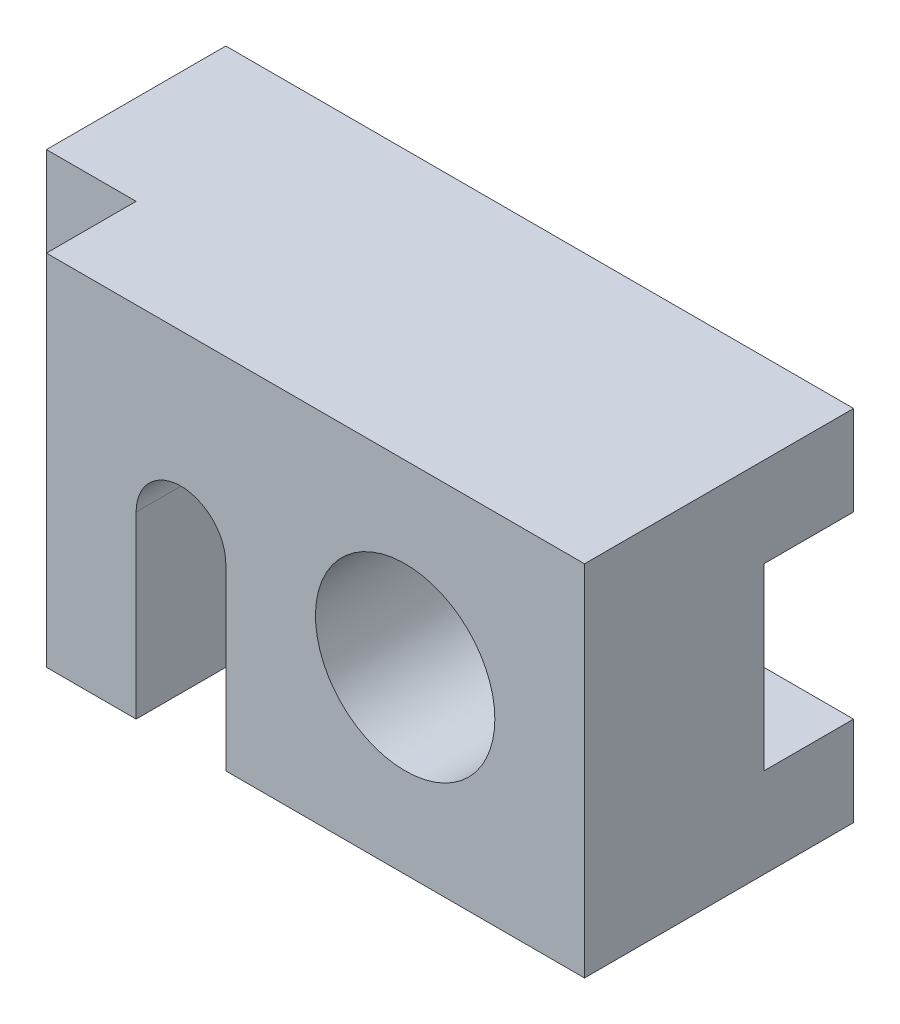
SolidWorks part; units mm, degrees
ref_plane "Front Plane" through (0, 0, 0) normal (0, 0, 1) x (1, 0, 0)
ref_plane "Top Plane" through (0, 0, 0) normal (0, 1, 0) x (1, 0, 0)
ref_plane "Right Plane" through (0, 0, 0) normal (1, 0, 0) x (0, 0, -1)
sketch "Sketch1" plane through (0, 0, 0) normal (0, 0, 1) x (1, 0, 0)
  line L0 (-11.602, 24) -> (88.4904, 24) construction
  line L1 (0, 0) -> (84, 0)
  line L2 (0, 0) -> (0, 48)
  line L3 (0, 48) -> (84, 48)
  line L4 (84, 0) -> (84, 48)
  line L5 (24, 24) -> (24, 0)
  line L6 (36, 24) -> (36, 0)
  line L8 (24, 12) -> (36, 12)
  line L9 (24, 0) -> (39.3883, 0)
  circle A0 centre (60, 24) radius 12
  arc A1 (24, 24) -> (36, 24) centre (30, 24) cw
  dimension "D3" = 24
  dimension "D1" = 48
  dimension "D2" = 84
  dimension "D4" = 24
  dimension "D5" = 30
  dimension "D6" = 12
extrude "Boss-Extrude1" add sketch "Sketch1" along normal blind 36
sketch "Sketch2" plane through (0, 48, 0) normal (0, 1, 0) x (1, 0, 0)
  line L1 (0, -36) -> (12, -36)
  line L2 (0, -36) -> (0, -24)
  line L3 (0, -24) -> (12, -24)
  line L4 (12, -36) -> (12, -24)
  dimension "D1" = 12
  dimension "D2" = 12
extrude "Cut-Extrude1" cut sketch "Sketch2" against normal through all
sketch "Sketch3" plane through (0, 0, 0) normal (-1, 0, 0) x (0, 0, 1)
  line L0 (0, 0) -> (0, 48) construction
  line L1 (0, 36) -> (12, 36)
  line L2 (0, 36) -> (0, 12)
  line L3 (0, 12) -> (12, 12)
  line L4 (12, 36) -> (12, 12)
  dimension "D1" = 24
  dimension "D3" = 12
extrude "Cut-Extrude2" cut sketch "Sketch3" against normal through all
sketch "Sketch5" plane through (0, 0, 36) normal (0, 0, 1) x (1, 0, 0)
  line L0 (12, 0) -> (84, 0) construction
  line L1 (24, 12) -> (36, 12)
  line L2 (24, 12) -> (24, 0)
  line L3 (24, 0) -> (36, 0)
  line L4 (36, 12) -> (36, 0)
  dimension "D1" = 12
extrude "Cut-Extrude4" cut sketch "Sketch5" against normal blind 24
